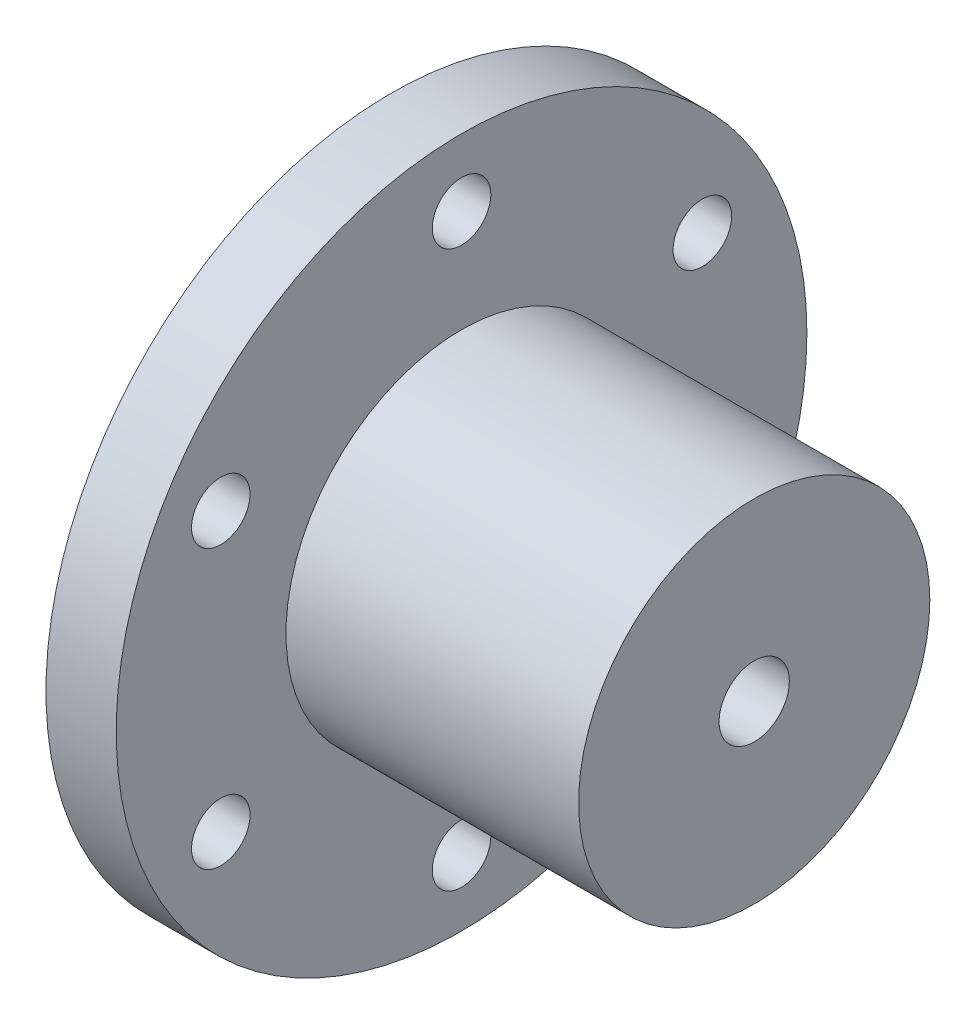
SolidWorks part; units mm, degrees
ref_plane "Front Plane" through (0, 0, 0) normal (0, 0, 1) x (1, 0, 0)
ref_plane "Top Plane" through (0, 0, 0) normal (0, 1, 0) x (1, 0, 0)
ref_plane "Right Plane" through (0, 0, 0) normal (1, 0, 0) x (0, 0, -1)
sketch "Sketch1" plane through (0, 0, 0) normal (1, 0, 0) x (0, 0, -1)
  circle A0 centre (0, 0) radius 15 construction
  circle A1 centre (0, 0) radius 23.75 construction
  circle A2 centre (0, 0) radius 29.5
extrude "Boss-Extrude1" add sketch "Sketch1" along normal blind 6
sketch "Sketch2" plane through (6, 0, 0) normal (1, 0, 0) x (0, 0, -1)
  circle A0 centre (0, 0) radius 15
extrude "Boss-Extrude2" add sketch "Sketch2" along normal blind 25
sketch "Sketch3" plane through (31, 0, 0) normal (1, 0, 0) x (0, 0, -1)
  circle A0 centre (0, 0) radius 3
extrude "Cut-Extrude1" cut sketch "Sketch3" against normal blind 25
sketch "Sketch4" plane through (6, 0, 0) normal (1, 0, 0) x (0, 0, -1)
  line L0 (0, 30.8547) -> (0, -31.0948) construction
  circle A0 centre (0, 0) radius 23.75 construction
  circle A1 centre (0, 23.75) radius 2.5
  circle A2 centre (20.5681, 11.875) radius 2.5
  circle A3 centre (20.5681, -11.875) radius 2.5
  circle A4 centre (0, -23.75) radius 2.5
  circle A5 centre (-20.5681, -11.875) radius 2.5
  circle A6 centre (-20.5681, 11.875) radius 2.5
  dimension "D1" = 6
extrude "Cut-Extrude2" cut sketch "Sketch4" against normal blind 25
